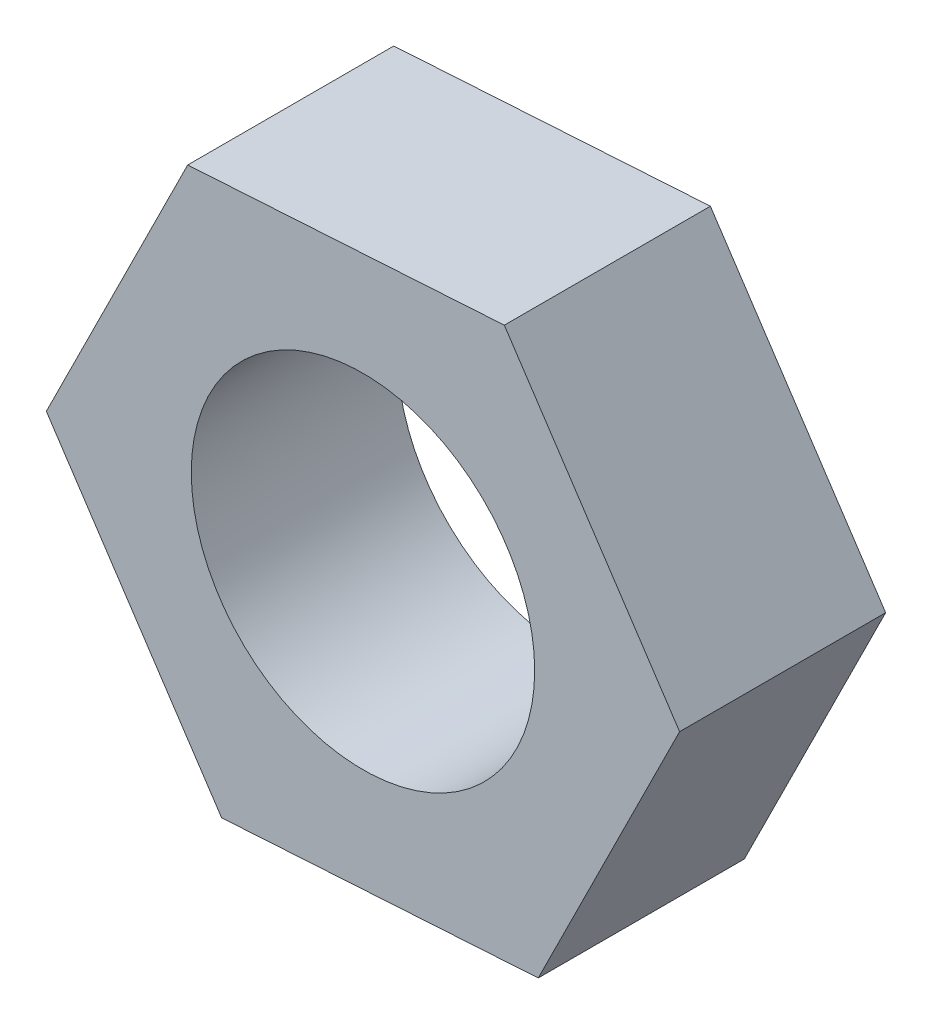
SolidWorks part; units mm, degrees
ref_plane "前基準面" through (0, 0, 0) normal (0, 0, 1) x (1, 0, 0)
ref_plane "上基準面" through (0, 0, 0) normal (0, 1, 0) x (1, 0, 0)
ref_plane "右基準面" through (0, 0, 0) normal (1, 0, 0) x (0, 0, -1)
sketch "草圖1" plane through (0, 0, 0) normal (0, 0, 1) x (1, 0, 0)
  line L1 (2.058, 4.1349) -> (-2.5519, 3.8498)
  line L2 (-2.5519, 3.8498) -> (-4.61, -0.2852)
  line L3 (-4.61, -0.2852) -> (-2.058, -4.1349)
  line L4 (-2.058, -4.1349) -> (2.5519, -3.8498)
  line L5 (2.5519, -3.8498) -> (4.61, 0.2852)
  line L6 (4.61, 0.2852) -> (2.058, 4.1349)
  circle A0 centre (0, 0) radius 4 construction
extrude "填料-伸長1" add sketch "草圖1" along normal blind 3
sketch "草圖2" plane through (0, 0, 3) normal (0, 0, 1) x (1, 0, 0)
  circle A0 centre (0, 0) radius 2.5
  dimension "D1" = 5
extrude "除料-伸長1" cut sketch "草圖2" against normal up to next
